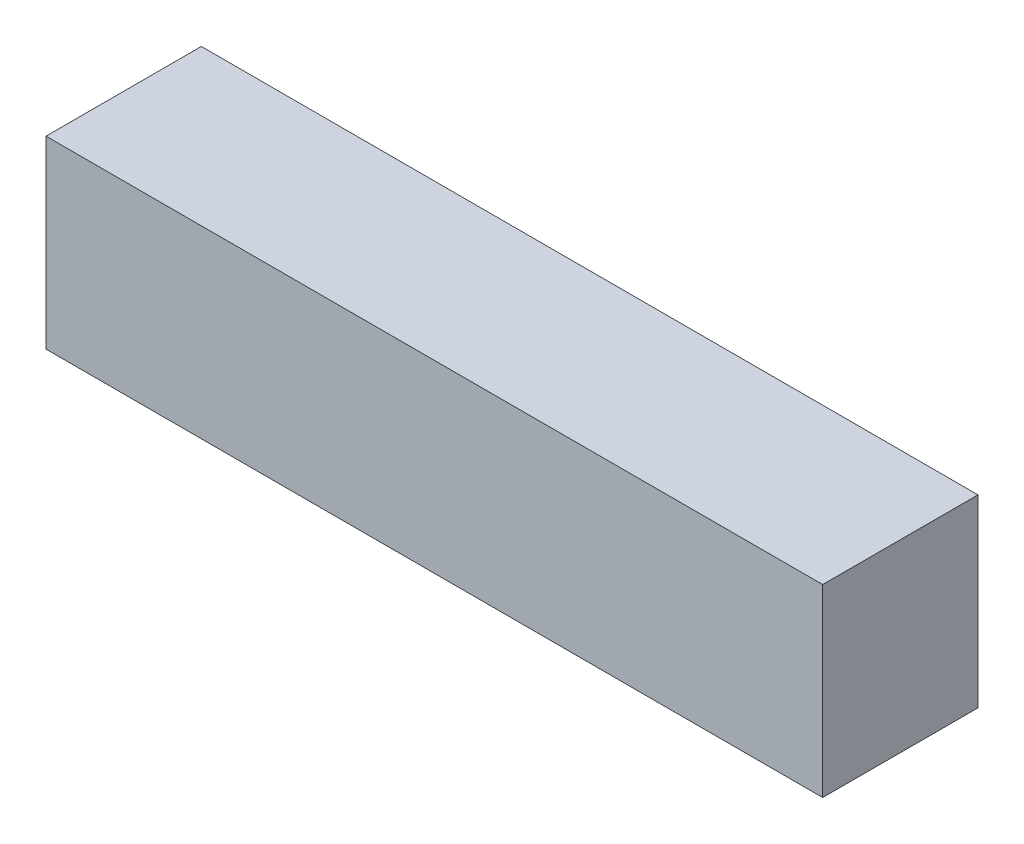
SolidWorks part; units mm, degrees
ref_plane "Front Plane" through (0, 0, 0) normal (0, 0, 1) x (1, 0, 0)
ref_plane "Top Plane" through (0, 0, 0) normal (0, 1, 0) x (1, 0, 0)
ref_plane "Right Plane" through (0, 0, 0) normal (1, 0, 0) x (0, 0, -1)
sketch "Sketch1" plane through (0, 0, 0) normal (0, 1, 0) x (1, 0, 0)
  line L1 (0, 0) -> (12192, 0)
  line L2 (0, 0) -> (0, -2438.4)
  line L3 (0, -2438.4) -> (12192, -2438.4)
  line L4 (12192, 0) -> (12192, -2438.4)
  dimension "D1" = 12192
  dimension "D2" = 2438.4
extrude "Boss-Extrude1" add sketch "Sketch1" along normal blind 2895.6
ref_plane "Plane1" through (76.2, 0, 0) normal (-1, 0, 0) x (0, 0, 1)
sketch "Sketch2" plane through (76.2, 0, 0) normal (-1, 0, 0) x (0, 0, 1)
  line L0 (0, 2895.6) -> (0, 0) construction
  line L1 (50.8, 2743.2) -> (2387.6, 2743.2)
  line L2 (50.8, 2743.2) -> (50.8, 152.4)
  line L3 (50.8, 152.4) -> (2387.6, 152.4)
  line L4 (2387.6, 2743.2) -> (2387.6, 152.4)
  line L5 (2438.4, 2895.6) -> (2438.4, 0) construction
  line L6 (0, 2895.6) -> (2438.4, 2895.6) construction
  line L7 (0, 0) -> (2438.4, 0) construction
  dimension "D1" = 50.8
  dimension "D2" = 50.8
  dimension "D3" = 152.4
  dimension "D4" = 152.4
extrude "Cut-Extrude1" cut sketch "Sketch2" against normal blind 12039.6
